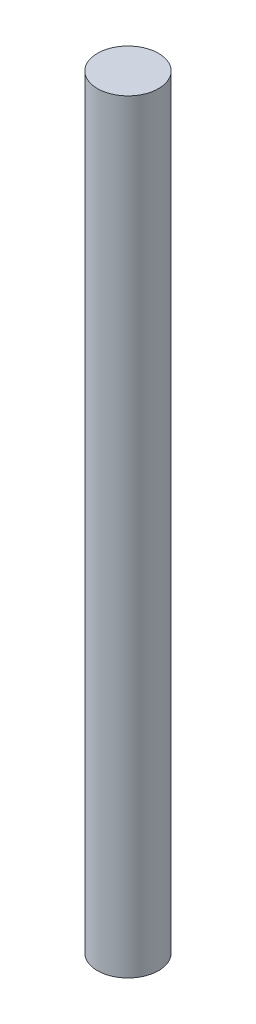
SolidWorks part; units mm, degrees
ref_plane "Front Plane" through (0, 0, 0) normal (0, 0, 1) x (1, 0, 0)
ref_plane "Top Plane" through (0, 0, 0) normal (0, 1, 0) x (1, 0, 0)
ref_plane "Right Plane" through (0, 0, 0) normal (1, 0, 0) x (0, 0, -1)
sketch "Croquis1" plane through (0, 0, 0) normal (0, 1, 0) x (1, 0, 0)
  circle A0 centre (0, 0) radius 4
  dimension "D1" = 8
extrude "Saliente-Extruir1" add sketch "Croquis1" along normal blind 100
